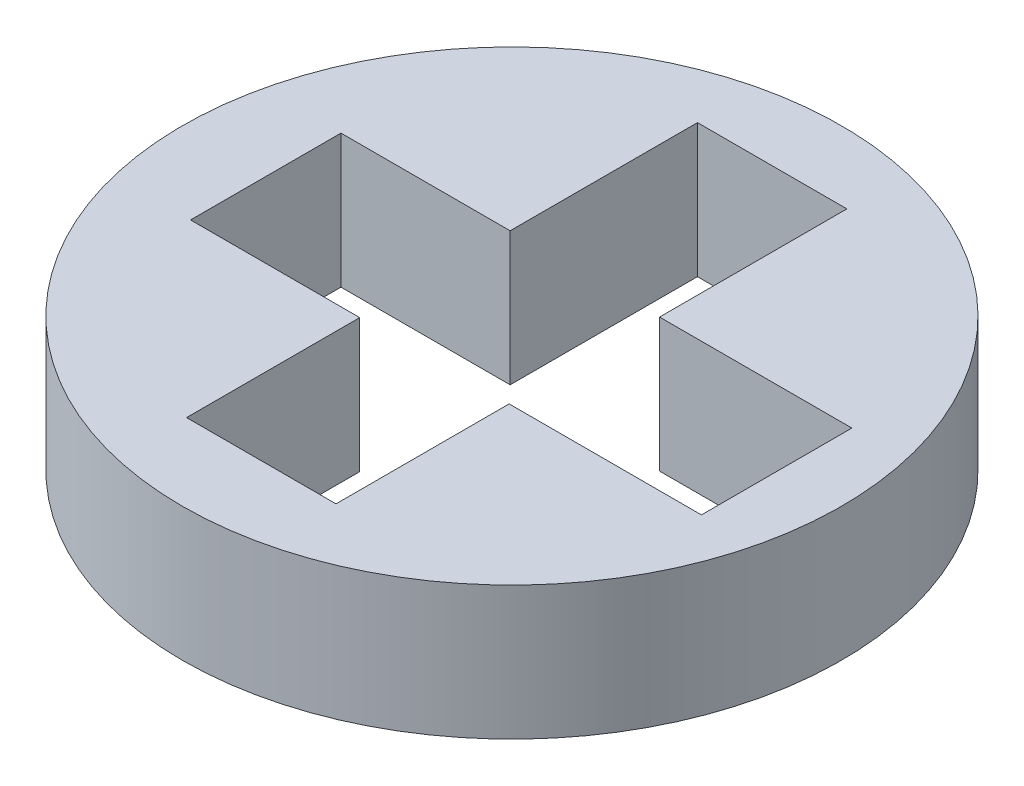
SolidWorks part; units mm, degrees
ref_plane "Front" through (0, 0, 0) normal (0, 0, 1) x (1, 0, 0)
ref_plane "Top" through (0, 0, 0) normal (0, 1, 0) x (1, 0, 0)
ref_plane "Right" through (0, 0, 0) normal (1, 0, 0) x (0, 0, -1)
sketch "Sketch1" plane through (0, 0, 0) normal (0, 1, 0) x (1, 0, 0)
  line L1 (-1.8278, 0.5465) -> (2.0012, 0.5465)
  line L2 (-1.8278, 0.5465) -> (-1.8278, -0.5808)
  line L3 (-1.8278, -0.5808) -> (2.0012, -0.5808)
  line L4 (2.0012, 0.5465) -> (2.0012, -0.5808)
  line L5 (-1.8278, 0.5465) -> (2.0012, -0.5808) construction
  line L6 (-1.8278, -0.5808) -> (2.0012, 0.5465) construction
  line L7 (-0.56, 1.9504) -> (0.56, 1.9504)
  line L8 (-0.56, 1.9504) -> (-0.56, -1.8786)
  line L9 (-0.56, -1.8786) -> (0.56, -1.8786)
  line L10 (0.56, 1.9504) -> (0.56, -1.8786)
  line L11 (-0.56, 1.9504) -> (0.56, -1.8786) construction
  line L12 (-0.56, -1.8786) -> (0.56, 1.9504) construction
  circle A0 centre (0, 0) radius 2.47
  point P7 (0.0867, -0.0172)
  point P12 (0, 0.0359)
extrude "Boss-Extrude1" add sketch "Sketch1" along normal blind 1 contours A0 L7 L10 L1 L4 L3 L9 L8 L2
